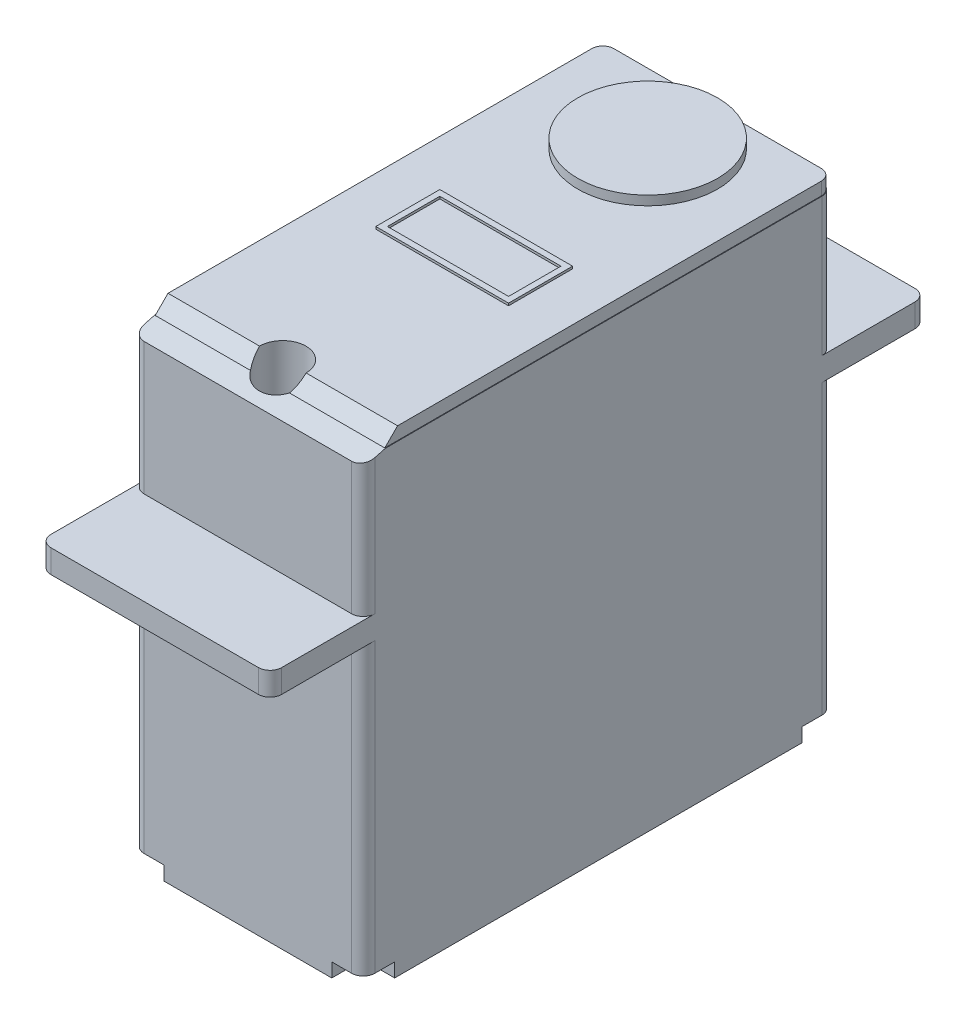
SolidWorks part; units mm, degrees
ref_plane "Plan de face" through (0, 0, 0) normal (0, 0, 1) x (1, 0, 0)
ref_plane "Plan de dessus" through (0, 0, 0) normal (0, 1, 0) x (1, 0, 0)
ref_plane "Plan de droite" through (0, 0, 0) normal (1, 0, 0) x (0, 0, -1)
sketch "Esquisse1" plane through (0, 0, 0) normal (1, 0, 0) x (0, 0, -1)
  line L1 (20.193, -20.447) -> (-20.193, -20.447)
  line L2 (20.193, -20.447) -> (20.193, 20.447)
  line L3 (20.193, 20.447) -> (-20.193, 20.447)
  line L4 (-20.193, -20.447) -> (-20.193, 20.447)
  line L5 (20.193, -20.447) -> (-20.193, 20.447) construction
  line L6 (20.193, 20.447) -> (-20.193, -20.447) construction
  point P0 (0, 0)
  dimension "D1" = 40.894
  dimension "D2" = 40.386
extrude "Boss.-Extru.1" add sketch "Esquisse1" along normal mid plane 19.812
sketch "Esquisse3" plane through (9.906, 0, 0) normal (1, 0, 0) x (0, 0, -1)
  line L0 (-20.193, -20.447) -> (20.193, -20.447) construction
  line L5 (0, 0) -> (0, 20.447) construction
  line L11 (20.193, 20.447) -> (-20.193, 20.447) construction
  line L12 (-20.193, 20.447) -> (-20.193, -20.447) construction
  line L13 (-20.193, 7.493) -> (-28.194, 7.493)
  line L14 (-20.193, 7.493) -> (-20.193, 5.493)
  line L15 (-20.193, 5.493) -> (-28.194, 5.493)
  line L16 (-28.194, 7.493) -> (-28.194, 5.493)
  line L17 (20.193, 5.493) -> (28.194, 5.493)
  line L18 (20.193, 7.493) -> (20.193, 5.493)
  line L19 (20.193, 7.493) -> (28.194, 7.493)
  line L20 (28.194, 7.493) -> (28.194, 5.493)
  dimension "D1" = 2
  dimension "D2" = 8.001
  dimension "D3" = 25.94
extrude "Boss.-Extru.2" add sketch "Esquisse3" against normal up to surface (19.812 mm away) up to face at (-9.906, 0, 0)
sketch "Esquisse6" plane through (0, 7.493, 0) normal (0, 1, 0) x (1, 0, 0)
  line L0 (0, 0) -> (9.906, 0) construction
  line L1 (9.906, 20.193) -> (9.906, -20.193) construction
  circle A0 centre (0, 17.2) radius 2
  circle A1 centre (0, -17.2) radius 2
  dimension "D1" = 4
  dimension "D2" = 34.4
extrude "Enlèv. mat.-Extru.1" cut sketch "Esquisse6" against normal through all both and the other way through all
sketch "Esquisse5" plane through (0, 20.447, 0) normal (0, 1, 0) x (1, 0, 0)
  line L1 (9.906, 20.193) -> (-9.906, 20.193) construction
  circle A0 centre (0, 14.143) radius 6
  dimension "D1" = 12
  dimension "D3" = 6.05
extrude "Boss.-Extru.3" add sketch "Esquisse5" along normal blind 0.8 contours A0
fillet "Congé2" radius 1 12 edges at (-9.906, 6.493, -28.194) (9.906, 6.493, -28.194) (-9.906, 13.97, -20.193) (9.906, 13.97, -20.193) (-9.906, -7.477, -20.193) (9.906, -7.477, -20.193) (-9.906, -7.477, 20.193) (9.906, -7.477, 20.193) (-9.906, 13.97, 20.193) (9.906, 13.97, 20.193) (-9.906, 6.493, 28.194) (9.906, 6.493, 28.194)
sketch "Esquisse7" plane through (0, 20.447, 0) normal (0, 1, 0) x (1, 0, 0)
  line L8 (8.906, 20.143) -> (-8.906, 20.143)
  line L9 (-9.856, 19.193) -> (-9.856, -19.193)
  line L10 (-8.906, -20.143) -> (8.906, -20.143)
  line L11 (9.856, -19.193) -> (9.856, 19.193)
  line L12 (8.906, 20.143) -> (-8.906, 20.143)
  line L13 (-9.856, 19.193) -> (-9.856, -19.193)
  line L14 (-8.906, -20.143) -> (8.906, -20.143)
  line L15 (9.856, -19.193) -> (9.856, 19.193)
  line L16 (8.906, 20.193) -> (-8.906, 20.193)
  line L17 (-9.906, 19.193) -> (-9.906, -19.193)
  line L18 (-8.906, -20.193) -> (8.906, -20.193)
  line L19 (9.906, -19.193) -> (9.906, 19.193)
  line L20 (8.906, 20.193) -> (-8.906, 20.193)
  line L21 (-9.906, 19.193) -> (-9.906, -19.193)
  line L22 (-8.906, -20.193) -> (8.906, -20.193)
  line L23 (9.906, -19.193) -> (9.906, 19.193)
  arc A8 (-8.906, 20.143) -> (-9.856, 19.193) centre (-8.906, 19.193) ccw
  arc A9 (-9.856, -19.193) -> (-8.906, -20.143) centre (-8.906, -19.193) ccw
  arc A10 (8.906, -20.143) -> (9.856, -19.193) centre (8.906, -19.193) ccw
  arc A11 (9.856, 19.193) -> (8.906, 20.143) centre (8.906, 19.193) ccw
  arc A12 (-8.906, 20.143) -> (-9.856, 19.193) centre (-8.906, 19.193) ccw
  arc A13 (-9.856, -19.193) -> (-8.906, -20.143) centre (-8.906, -19.193) ccw
  arc A14 (8.906, -20.143) -> (9.856, -19.193) centre (8.906, -19.193) ccw
  arc A15 (9.856, 19.193) -> (8.906, 20.143) centre (8.906, 19.193) ccw
  arc A16 (-8.906, 20.193) -> (-9.906, 19.193) centre (-8.906, 19.193) ccw
  arc A17 (-9.906, -19.193) -> (-8.906, -20.193) centre (-8.906, -19.193) ccw
  arc A18 (8.906, -20.193) -> (9.906, -19.193) centre (8.906, -19.193) ccw
  arc A19 (9.906, 19.193) -> (8.906, 20.193) centre (8.906, 19.193) ccw
  arc A20 (-8.906, 20.193) -> (-9.906, 19.193) centre (-8.906, 19.193) ccw
  arc A21 (-9.906, -19.193) -> (-8.906, -20.193) centre (-8.906, -19.193) ccw
  arc A22 (8.906, -20.193) -> (9.906, -19.193) centre (8.906, -19.193) ccw
  arc A23 (9.906, 19.193) -> (8.906, 20.193) centre (8.906, 19.193) ccw
  dimension "D1" = 0.05
  dimension "D2" = 0
extrude "Enlèv. mat.-Extru.2" cut sketch "Esquisse7" against normal blind 1.1
sketch "Esquisse8" plane through (9.906, 0, 0) normal (1, 0, 0) x (0, 0, -1)
  line L0 (-17.193, 20.447) -> (-18.293, 19.347)
  line L1 (-19.193, 20.447) -> (19.193, 20.447) construction
  line L2 (-19.193, 19.347) -> (19.193, 19.347) construction
  line L3 (-18.293, 19.347) -> (-20.193, 18.8379)
  line L4 (-20.193, 7.493) -> (-20.193, 19.347) construction
  line L5 (-20.193, 18.8379) -> (-20.193, 20.447)
  line L6 (-20.193, 20.447) -> (-17.193, 20.447)
  dimension "D1" = 45
  dimension "D2" = 3
  dimension "D3" = 150
extrude "Enlèv. mat.-Extru.3" cut sketch "Esquisse8" against normal through all both and the other way through all
sketch "Esquisse9" plane through (0, 20.447, 0) normal (0, 1, 0) x (1, 0, 0)
  line L0 (0, -0.757) -> (0, 0) construction
  line L1 (-5.7, 1.993) -> (5.7, 1.993)
  line L2 (-5.7, 1.993) -> (-5.7, -3.507)
  line L3 (-5.7, -3.507) -> (5.7, -3.507)
  line L4 (5.7, 1.993) -> (5.7, -3.507)
  line L5 (-5.7, 1.993) -> (5.7, -3.507) construction
  line L6 (-5.7, -3.507) -> (5.7, 1.993) construction
  line L7 (8.906, 20.143) -> (0, 20.143) construction
  point P0 (0, -0.757)
  dimension "D1" = 11.4
  dimension "D2" = 5.5
  dimension "D3" = 23.65
extrude "Extru.-Mince1" add sketch "Esquisse9" along normal blind 0.2 thin
sketch "Esquisse10" plane through (0, 21.247, 0) normal (0, 1, 0) x (1, 0, 0)
  circle A0 centre (0, 14.143) radius 2.95
  dimension "D1" = 5.9
sketch "Esquisse13" plane through (0, -20.447, 0) normal (0, -1, 0) x (1, 0, 0)
  line L0 (-8.906, 20.193) -> (8.906, 20.193) construction
  line L1 (-7.206, 20.193) -> (-9.906, 20.193)
  line L2 (-7.206, 20.193) -> (-7.206, 18.993)
  line L3 (-8.706, 17.493) -> (-9.906, 17.493)
  line L4 (-9.906, 20.193) -> (-9.906, 17.493)
  line L5 (-9.906, 19.193) -> (-9.906, -19.193) construction
  line L6 (0, 20.193) -> (0, 0) construction
  line L7 (0, 0) -> (-9.906, 0) construction
  line L8 (9.906, 20.193) -> (9.906, 17.493)
  line L9 (8.706, 17.493) -> (9.906, 17.493)
  line L10 (7.206, 20.193) -> (7.206, 18.993)
  line L11 (7.206, 20.193) -> (9.906, 20.193)
  line L12 (7.206, -20.193) -> (9.906, -20.193)
  line L13 (7.206, -20.193) -> (7.206, -18.993)
  line L14 (8.706, -17.493) -> (9.906, -17.493)
  line L15 (9.906, -20.193) -> (9.906, -17.493)
  line L16 (-9.906, -20.193) -> (-9.906, -17.493)
  line L17 (-8.706, -17.493) -> (-9.906, -17.493)
  line L18 (-7.206, -20.193) -> (-7.206, -18.993)
  line L19 (-7.206, -20.193) -> (-9.906, -20.193)
  arc A0 (-7.206, 18.993) -> (-8.706, 17.493) centre (-8.706, 18.993) cw
  arc A1 (7.206, 18.993) -> (8.706, 17.493) centre (8.706, 18.993) ccw
  arc A2 (7.206, -18.993) -> (8.706, -17.493) centre (8.706, -18.993) cw
  arc A3 (-7.206, -18.993) -> (-8.706, -17.493) centre (-8.706, -18.993) ccw
  dimension "D2" = 1.5
  dimension "D1" = 2.7
extrude "Enlèv. mat.-Extru.4" cut sketch "Esquisse13" against normal blind 1.2 and the other way through all
hole_wizard "Trou pour taraudage pour trou taraudé M1.2x0.251" positions "Esquisse14" profile "Esquisse15" hole size "M1.2x0.25" standard "ISO"
sketch "Esquisse14" plane through (0, -19.247, 0) normal (0, -1, 0) x (-1, 0, 0)
  point P0 (-8.706, -18.993)
  point P8 (8.906, -19.193)
  point P11 (-8.706, 18.993)
  point P14 (8.906, 19.193)
sketch "Esquisse15" plane through (8.706, -19.247, 18.993) normal (1, 0, 0) x (0, 0, -1)
  line L0 (0, 0) -> (0, 5)
  line L1 (0, 5) -> (0.475, 4.7146)
  line L2 (0.475, 4.7146) -> (0.475, 0)
  line L5 (0.475, 0) -> (0, 0)
  line L10 (0, 5) -> (-0.475, 4.7146) construction
  line L11 (0, -6.35) -> (0, 107.95) construction
  dimension "Diamètre du perçage" = 0.95
  dimension "Profondeur du perçage" = 5
  dimension "Angle de pointe" = 118
sketch "Esquisse16" plane through (0, 0, -20.193) normal (0, 0, -1) x (-1, 0, 0)
  line L0 (0, 0) -> (0, -15.047) construction
  line L1 (-1.8, -15.047) -> (1.8, -15.047)
  line L2 (-1.8, -15.047) -> (-1.8, -16.347)
  line L3 (-1.8, -16.347) -> (1.8, -16.347)
  line L4 (1.8, -15.047) -> (1.8, -16.347)
  line L5 (-7.206, -20.447) -> (7.206, -20.447) construction
  dimension "D1" = 3.6
  dimension "D2" = 1.3
  dimension "D3" = 5.4
extrude "Enlèv. mat.-Extru.5" cut sketch "Esquisse16" against normal blind 5
sketch "Esquisse17" plane through (0, 0, -15.193) normal (0, 0, -1) x (-1, 0, 0)
  line L0 (-1.8, -15.697) -> (1.8, -15.697) construction
  line L1 (-1.8, -15.047) -> (-1.8, -16.347) construction
  line L2 (1.8, -16.347) -> (1.8, -15.047) construction
  circle A0 centre (0, -15.697) radius 0.625
  circle A1 centre (-1.25, -15.697) radius 0.625
  circle A2 centre (1.25, -15.697) radius 0.625
  line M3 (-1.8, -15.047) -> (-1.8, -16.347)
  line M5 (1.8, -16.347) -> (1.8, -15.047)
  dimension "D1" = 1.25
extrude "Boss.-Extru.5" add sketch "Esquisse17" along normal blind 10 separate body contours L0 A2 M5 | L0 A0 | L0 A1 M3 | L0 A1 M3 | A0 L0 | A2 L0 M5 | A1 M3 | A2 M5
